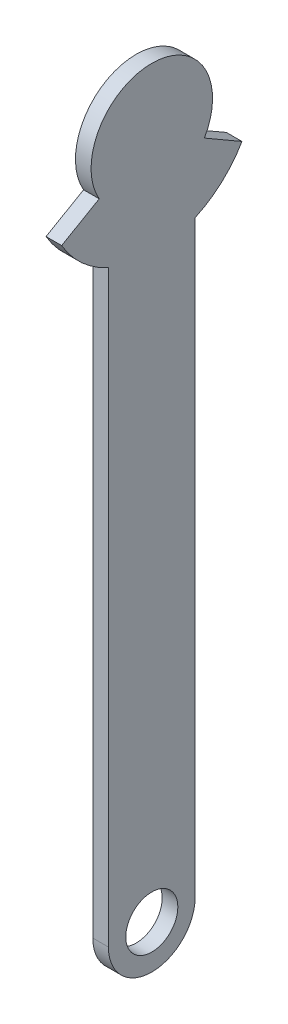
SolidWorks part; units mm, degrees
material "6061 Alloy"
ref_plane "Front Plane" through (0, 0, 0) normal (0, 0, 1) x (1, 0, 0)
ref_plane "Top Plane" through (0, 0, 0) normal (0, 1, 0) x (1, 0, 0)
ref_plane "Right Plane" through (0, 0, 0) normal (1, 0, 0) x (0, 0, -1)
sketch "Sketch1" plane through (0, 0, 0) normal (1, 0, 0) x (0, 0, -1)
  line L0 (0, -196.8) -> (0, 136.8) construction
  line L1 (30.3109, 179.3) -> (51.9615, 166.8)
  line L2 (-25, 142.2564) -> (-25, -196.8)
  line L3 (25, 142.2564) -> (25, -196.8)
  line L4 (-30.3109, 179.3) -> (-51.9615, 166.8)
  line L6 (0, 161.8) -> (0, 196.8) construction
  arc A0 (-51.9615, 166.8) -> (-25, 142.2564) centre (0, 196.8) ccw
  arc A1 (30.3109, 179.3) -> (-30.3109, 179.3) centre (0, 196.8) ccw
  arc A2 (-25, -196.8) -> (25, -196.8) centre (0, -196.8) ccw
  arc A3 (25, 142.2564) -> (51.9615, 166.8) centre (0, 196.8) ccw
  circle A4 centre (0, -196.8) radius 15
  point P4 (0, 0)
  point P9 (0, 196.8)
  dimension "D2" = 120
  dimension "D3" = 70
  dimension "D4" = 30
  dimension "D1" = 393.6
extrude "Boss-Extrude1" add sketch "Sketch1" along normal blind 9
